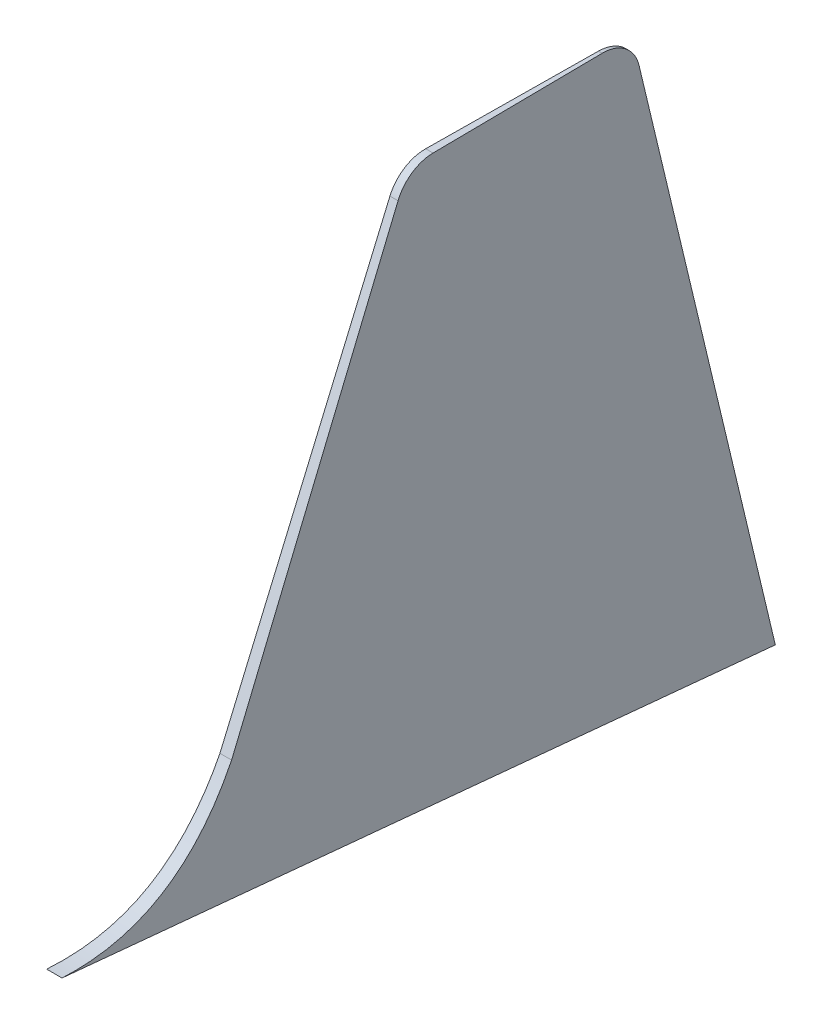
SolidWorks part; units mm, degrees
ref_plane "Front Plane" through (0, 0, 0) normal (0, 0, 1) x (1, 0, 0)
ref_plane "Top Plane" through (0, 0, 0) normal (0, 1, 0) x (1, 0, 0)
ref_plane "Right Plane" through (0, 0, 0) normal (1, 0, 0) x (0, 0, -1)
sketch "Sketch1" plane through (0, 0, 0) normal (1, 0, 0) x (0, 0, -1)
  line L0 (2128.0444, -2196.748) -> (3318.7111, -2196.748) construction
  line L6 (274.5084, 659.691) -> (1726.7925, 506.9369)
  line L7 (1726.7925, 506.9369) -> (1457.5195, 1623.9937)
  line L8 (1384.608, 1681.418) -> (1050.4408, 1681.418)
  line L9 (981.3223, 1635.5323) -> (652.4466, 854.7689)
  arc A2 (1384.608, 1681.418) -> (1457.5195, 1623.9937) centre (1384.608, 1606.418) cw
  arc A3 (1050.4408, 1681.418) -> (981.3223, 1635.5323) centre (1050.4408, 1606.418) ccw
  spline S0 degree 2 poles (274.5084, 659.691) (535.2671, 621.4882) (652.4466, 854.7689) knots 0 0 0 1 1 1
  dimension "D1" = 75
extrude "Boss-Extrude2" add sketch "Sketch1" along normal blind 30 contours S0 L6 L7 A2 L8 A3 L9
sketch "Sketch2" plane through (0, 0, 0) normal (0, 1, 0) x (1, 0, 0)
  line L0 (15, 1726.7925) -> (0, 317.3323)
  line L1 (30, 1726.7925) -> (0, 1726.7925) construction
  line L2 (0, 317.3323) -> (30, 317.3323)
  line L3 (30, 317.3323) -> (15, 1726.7925)
extrude "Cut-Extrude3" cut sketch "Sketch2" along normal through all flip side to cut
